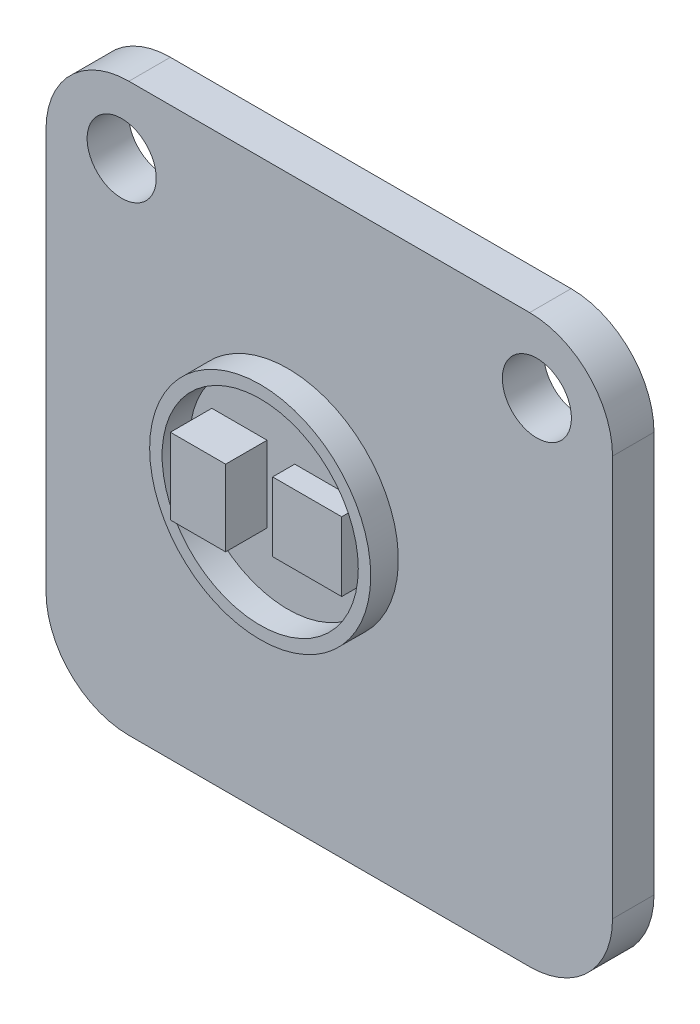
SolidWorks part; units mm, degrees
ref_plane "Front Plane" through (0, 0, 0) normal (0, 0, 1) x (1, 0, 0)
ref_plane "Top Plane" through (0, 0, 0) normal (0, 1, 0) x (1, 0, 0)
ref_plane "Right Plane" through (0, 0, 0) normal (1, 0, 0) x (0, 0, -1)
sketch "Sketch1" plane through (0, 0, 0) normal (0, 0, 1) x (1, 0, 0)
  line L1 (0, 0) -> (20.5, 0)
  line L2 (0, 0) -> (0, 20.5)
  line L3 (0, 20.5) -> (20.5, 20.5)
  line L4 (20.5, 0) -> (20.5, 20.5)
  dimension "D1" = 20.5
extrude "Boss-Extrude1" add sketch "Sketch1" along normal blind 1.5
fillet "Fillet1" radius 3 4 edges at (20.5, 0, 0.75) (0, 0, 0.75) (20.5, 20.5, 0.75) (0, 20.5, 0.75)
sketch "Sketch9" plane through (0, 0, 1.5) normal (0, 0, 1) x (1, 0, 0)
  line L0 (17.5, 20.5) -> (3, 20.5) construction
  line L3 (10.25, 20.5) -> (10.25, 0) construction
  line L4 (3, 0) -> (17.5, 0) construction
  circle A0 centre (2.7379, 17.95) radius 1.25
  arc A3 (3, 20.5) -> (0, 17.5) centre (3, 17.5) ccw construction
  circle A4 centre (17.7621, 17.95) radius 1.25
  point P7 (0.8787, 19.6213)
  dimension "D1" = 2.5
  dimension "D2" = 2.5
  dimension "D3" = 2.55
extrude "Cut-Extrude1" cut sketch "Sketch9" against normal blind 4.5 contours A4 | A0
sketch "Sketch10" plane through (0, 0, 1.5) normal (0, 0, 1) x (1, 0, 0)
  line L0 (10.25, 20.5) -> (10.25, 0) construction
  line L1 (9, 11.5) -> (11.5, 11.5)
  line L2 (9, 11.5) -> (9, 9)
  line L3 (9, 9) -> (11.5, 9)
  line L4 (11.5, 11.5) -> (11.5, 9)
  line L5 (9, 11.5) -> (11.5, 9) construction
  line L6 (9, 9) -> (11.5, 11.5) construction
  line L7 (17.5, 20.5) -> (3, 20.5) construction
  line L8 (3, 0) -> (17.5, 0) construction
  line L9 (0, 10.25) -> (20.5, 10.25) construction
  line L10 (0, 17.5) -> (0, 3) construction
  line L11 (20.5, 3) -> (20.5, 17.5) construction
  point P0 (10.25, 10.25)
  point P18 (10.25, 10.25)
  dimension "D1" = 2.5
  dimension "D2" = 2.5
extrude "Boss-Extrude2" add sketch "Sketch10" along normal blind 0.8
sketch "Sketch11" plane through (0, 0, 1.5) normal (0, 0, 1) x (1, 0, 0)
  line L0 (11.5, 9) -> (11.5, 11.5) construction
  line L1 (6, 11.75) -> (8, 11.75)
  line L2 (6, 11.75) -> (6, 9)
  line L3 (6, 9) -> (8, 9)
  line L4 (8, 11.75) -> (8, 9)
  line L6 (9, 9) -> (11.5, 9) construction
  dimension "D1" = 2.75
  dimension "D2" = 2
  dimension "D3" = 5.5
extrude "Boss-Extrude3" add sketch "Sketch11" along normal blind 1.5 contours L2 L1 L4 L3
sketch "Sketch12" plane through (0, 0, 1.5) normal (0, 0, 1) x (1, 0, 0)
  line L0 (8.75, 11.75) -> (8.75, 9) construction
  line L1 (6, 11.75) -> (11.5, 11.75)
  line L2 (6, 11.75) -> (6, 9)
  line L3 (6, 9) -> (11.5, 9)
  line L4 (11.5, 11.75) -> (11.5, 9)
  line L5 (6, 10.375) -> (11.5, 10.375) construction
  circle A0 centre (8.75, 10.375) radius 3.55
  circle A1 centre (8.75, 10.375) radius 4
  dimension "D1" = 7.1
extrude "Boss-Extrude4" add sketch "Sketch12" along normal blind 1 contours A1 A0
